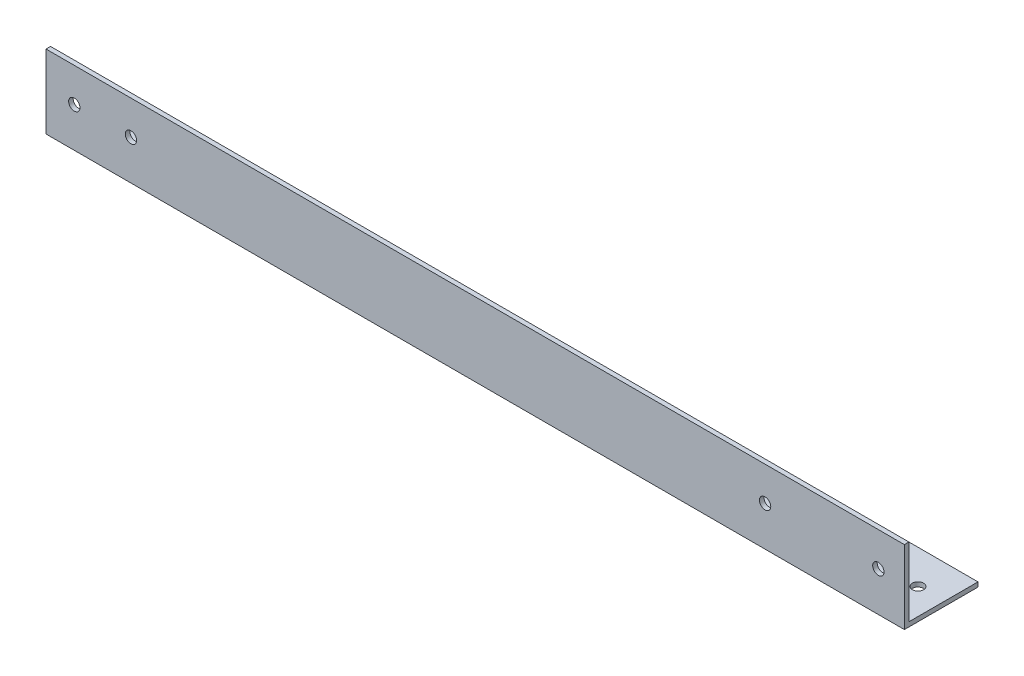
SolidWorks part; units mm, degrees
ref_plane "Спереди" through (0, 0, 0) normal (0, 0, 1) x (1, 0, 0)
ref_plane "Сверху" through (0, 0, 0) normal (0, 1, 0) x (1, 0, 0)
ref_plane "Справа" through (0, 0, 0) normal (1, 0, 0) x (0, 0, -1)
sketch "Эскиз1" plane through (0, 0, 0) normal (1, 0, 0) x (0, 0, -1)
  line L0 (0, 0) -> (0, 65)
  line L1 (0, 0) -> (65, 0)
extrude "Вытянуть-Тонкостенный1" add sketch "Эскиз1" along normal blind 758 thin
sketch "Эскиз2" plane through (0, 0, 0) normal (0, 0, 1) x (1, 0, 0)
  circle A0 centre (25, 35) radius 5
  circle A1 centre (75, 35) radius 5
  circle A2 centre (735, 35) radius 5
  circle A6 centre (635, 35) radius 5
  dimension "D2" = 2
  dimension "D1" = 2
extrude "Вырез-Вытянуть1" cut sketch "Эскиз2" against normal blind 10
sketch "Эскиз3" plane through (0, 0, 0) normal (0, -1, 0) x (1, 0, 0)
  circle A0 centre (25, -35) radius 5
  circle A1 centre (75, -35) radius 5
  circle A2 centre (735, -35) radius 5
  circle A6 centre (635, -35) radius 5
  dimension "D1" = 2
  dimension "D2" = 2
extrude "Вырез-Вытянуть2" cut sketch "Эскиз3" against normal blind 10
